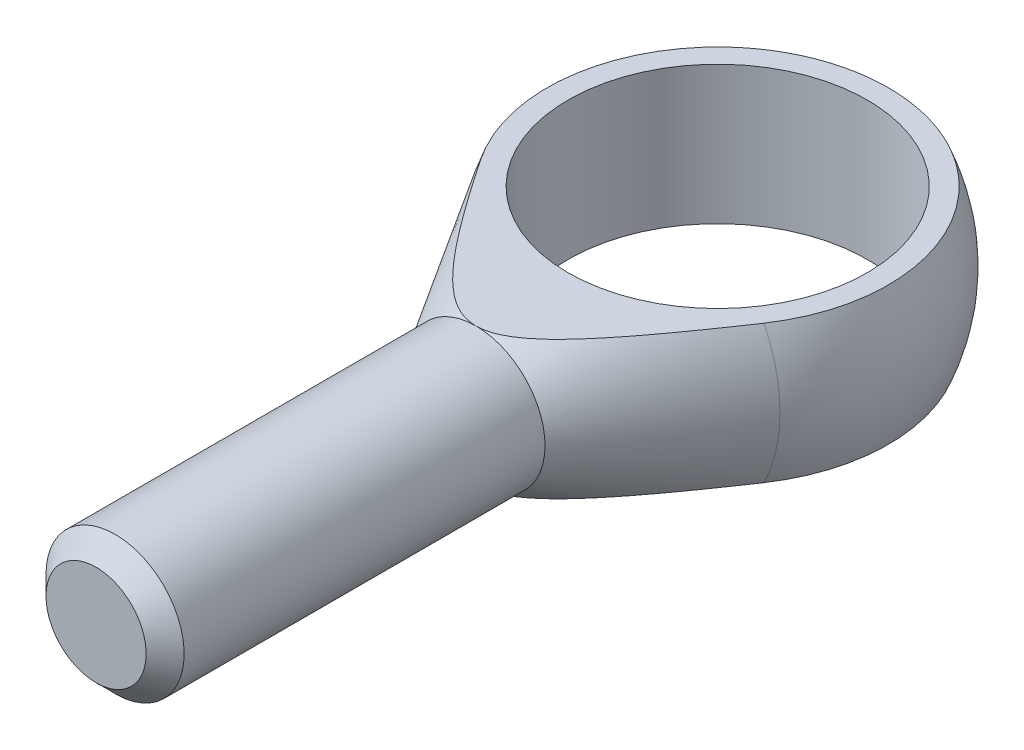
SolidWorks part; units mm, degrees
material "1.0545 (S355N)"
ref_plane "Płaszczyzna przednia" through (0, 0, 0) normal (0, 0, 1) x (1, 0, 0)
ref_plane "Płaszczyzna górna" through (0, 0, 0) normal (0, 1, 0) x (1, 0, 0)
ref_plane "Płaszczyzna prawa" through (0, 0, 0) normal (1, 0, 0) x (0, 0, -1)
sketch "Szkic1" plane through (0, 0, 0) normal (0, 1, 0) x (1, 0, 0)
  line L0 (0, 26.0435) -> (0, -71.4286) construction
  line L1 (-6, -54) -> (6, -54)
  line L2 (6, -54) -> (6, -21)
  line L3 (-6, -54) -> (-6, -21)
  line L4 (-13.6918, -8.2785) -> (-6, -21)
  line L5 (6, -21) -> (13.6918, -8.2785)
  line L6 (-6, -21) -> (6, -21)
  line L7 (0, 16) -> (0, -54)
  arc A0 (13.6918, -8.2785) -> (-13.6918, -8.2785) centre (0, 0) ccw
  point P7 (0, -54)
  dimension "d4" = 32
  dimension "d2" = 12
  dimension "l1" = 54
  dimension "l3" = 33
revolve "Obrót1" add sketch "Szkic1" angle 360 about L0
sketch "Szkic2" plane through (0, 0, 0) normal (1, 0, 0) x (0, 0, -1)
  line L4 (-21, 6) -> (14.8324, 6)
  line L5 (-21, -6) -> (14.8324, -6)
  line L6 (-21, -6) -> (-8.2785, -13.6918) construction
  line L7 (-8.2785, 13.6918) -> (-21, 6) construction
  line L8 (-21, -6) -> (-8.2785, -13.6918)
  line L9 (-8.2785, 13.6918) -> (-21, 6)
  arc A0 (-8.2785, -13.6918) -> (-8.2785, 13.6918) centre (0, 0) ccw construction
  arc A1 (-8.2785, -13.6918) -> (14.8324, -6) centre (0, 0) ccw
  arc A2 (14.8324, 6) -> (-8.2785, 13.6918) centre (0, 0) ccw
extrude "Wytnij-wyciągnięcie1" cut sketch "Szkic2" against normal through all both and the other way through all
sketch "Szkic3" plane through (0, 0, 0) normal (0, 1, 0) x (1, 0, 0)
  circle A0 centre (0, 0) radius 13
  dimension "b" = 26
extrude "Wytnij-wyciągnięcie2" cut sketch "Szkic3" against normal through all both and the other way through all contours A0
chamfer "Sfazowanie1" distance 1.65 angle 45 1 edges at (-6, 0, 54)
equation "\"D1@Sfazowanie1\"=\"l3@Szkic1\"*0.05"
